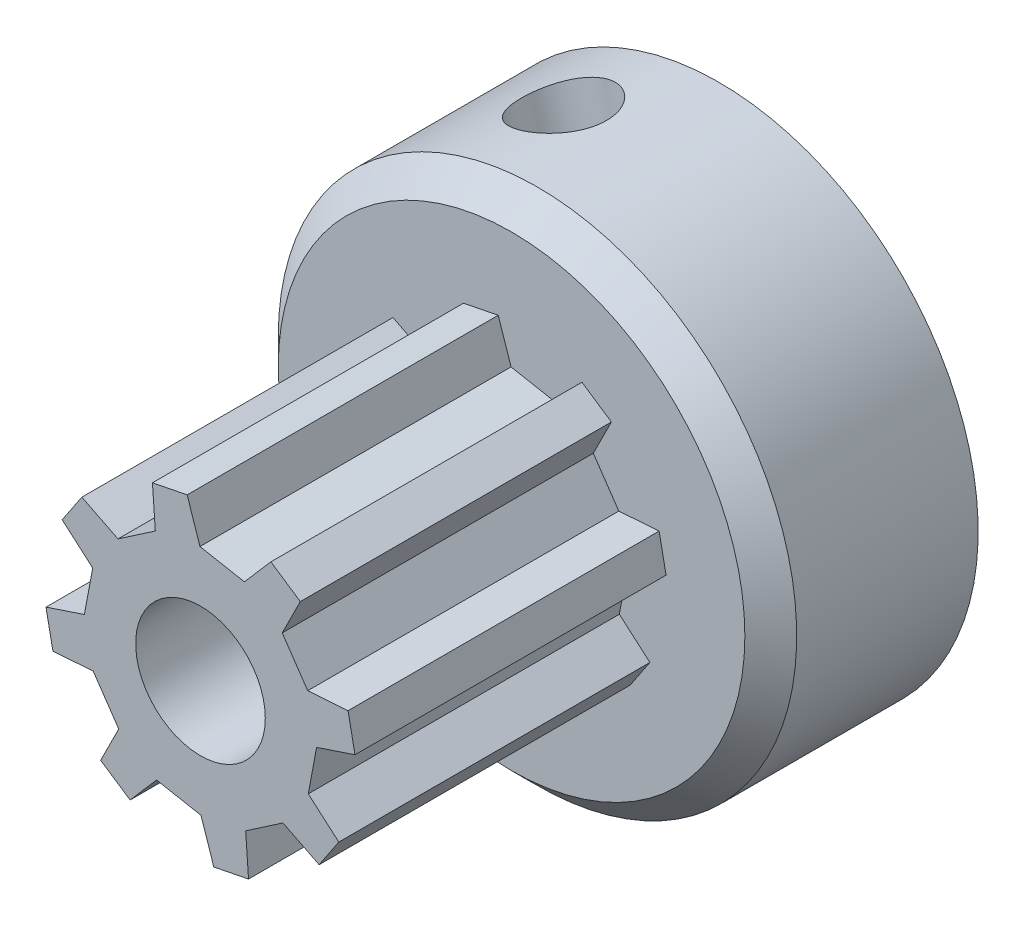
SolidWorks part; units mm, degrees
ref_plane "Front Plane" through (0, 0, 0) normal (0, 0, 1) x (1, 0, 0)
ref_plane "Top Plane" through (0, 0, 0) normal (0, 1, 0) x (1, 0, 0)
ref_plane "Right Plane" through (0, 0, 0) normal (1, 0, 0) x (0, 0, -1)
ref_plane "Plane1" through (0, 0, 15) normal (0, 0, 1) x (1, 0, 0)
sketch "Sketch1" plane through (0, 0, 15) normal (0, 0, 1) x (1, 0, 0)
  line L0 (-0.0203, 4.4797) -> (1.6934, 4.1575)
  line L1 (2.7151, 5.3359) -> (1.6934, 4.1575)
  line L2 (3.8511, 4.5768) -> (2.7151, 5.3359)
  line L3 (3.1533, 3.182) -> (3.8511, 4.5768)
  line L4 (3.1533, 3.182) -> (4.1372, 1.7424)
  line L5 (5.6929, 1.8532) -> (4.1372, 1.7424)
  line L6 (5.9594, 0.5132) -> (5.6929, 1.8532)
  line L7 (4.4797, 0.0203) -> (5.9594, 0.5132)
  line L8 (4.4797, 0.0203) -> (4.1575, -1.6934)
  line L9 (5.3359, -2.7151) -> (4.1575, -1.6934)
  line L10 (4.5768, -3.8511) -> (5.3359, -2.7151)
  line L11 (3.182, -3.1533) -> (4.5768, -3.8511)
  line L12 (3.182, -3.1533) -> (1.7424, -4.1372)
  line L13 (1.8532, -5.6929) -> (1.7424, -4.1372)
  line L14 (0.5132, -5.9594) -> (1.8532, -5.6929)
  line L15 (0.0203, -4.4797) -> (0.5132, -5.9594)
  line L16 (0.0203, -4.4797) -> (-1.6934, -4.1575)
  line L17 (-2.7151, -5.3359) -> (-1.6934, -4.1575)
  line L18 (-3.8511, -4.5768) -> (-2.7151, -5.3359)
  line L19 (-3.1533, -3.182) -> (-3.8511, -4.5768)
  line L20 (-3.1533, -3.182) -> (-4.1372, -1.7424)
  line L21 (-5.6929, -1.8532) -> (-4.1372, -1.7424)
  line L22 (-3.182, 3.1533) -> (-1.7424, 4.1372)
  line L23 (-5.9594, -0.5132) -> (-5.6929, -1.8532)
  line L24 (-4.4797, -0.0203) -> (-5.9594, -0.5132)
  line L25 (-4.4797, -0.0203) -> (-4.1575, 1.6934)
  line L26 (-5.3359, 2.7151) -> (-4.1575, 1.6934)
  line L27 (-4.5768, 3.8511) -> (-5.3359, 2.7151)
  line L28 (-3.182, 3.1533) -> (-4.5768, 3.8511)
  line L29 (-1.1832, 5.8262) -> (-1.2808, 6.3166) construction
  line L30 (3.2831, 4.9564) -> (3.5592, 5.3732) construction
  line L31 (-1.2808, 6.3166) -> (3.5592, 5.3732) construction
  line L32 (-4.9912, 3.3063) -> (-5.4069, 3.5841) construction
  line L33 (-5.8262, -1.1832) -> (-6.3572, -1.2911) construction
  line L34 (-6.3572, -1.2911) -> (-5.4069, 3.5841) construction
  line L104 (-0.0203, 4.4797) -> (-0.5132, 5.9594)
  line L105 (-0.5132, 5.9594) -> (-1.8532, 5.6929)
  line L106 (-1.8532, 5.6929) -> (-1.7424, 4.1372)
  circle A0 centre (0, 0) radius 2.5
  circle A1 centre (0, 0) radius 6.4451 construction
  circle A2 centre (0, 0) radius 5.9869 construction
  circle A3 centre (0, 0) radius 6.4869 construction
  dimension "D4" = 5.097
  dimension "D1" = 97.174
  dimension "D2" = 97.174
  dimension "D3" = 8
extrude "Boss-Extrude1" add sketch "Sketch1" against normal blind 12
sketch "Sketch2" plane through (0, 0, 3) normal (0, 0, -1) x (-1, 0, 0)
  circle A0 centre (0, 0) radius 10
extrude "Boss-Extrude2" add sketch "Sketch2" along normal blind 8
sketch "Sketch9" plane through (0, 0, -5) normal (0, 0, -1) x (-1, 0, 0)
  line L0 (3.8021, 2.565) -> (4.5859, 5.4608)
  line L2 (4.5859, 5.4608) -> (-1.2058, 7.0283)
  line L3 (1.6901, 6.2445) -> (-0.9644, 6.9629) construction
  line L5 (-1.9895, 4.1324) -> (3.8021, 2.565)
  line L8 (-1.2058, 7.0283) -> (-1.9895, 4.1324)
  line L10 (-1.7482, 4.0671) -> (3.5608, 2.6303) construction
  line L11 (1.6901, 6.2445) -> (4.3446, 5.5261) construction
  line L12 (3.7368, 2.3236) -> (4.6512, 5.7021) construction
  line L13 (-2.0548, 3.8911) -> (3.7368, 2.3236) construction
  line L14 (-1.1404, 7.2696) -> (-2.0548, 3.8911) construction
  line L15 (3.5608, 2.6303) -> (4.3446, 5.5261) construction
  line L16 (-0.9644, 6.9629) -> (-1.7482, 4.0671) construction
  line L17 (1.7554, 6.4858) -> (-1.1404, 7.2696) construction
  line L18 (1.7554, 6.4858) -> (4.6512, 5.7021) construction
  dimension "D2" = 0.25
extrude "Cut-Extrude5" cut sketch "Sketch9" against normal blind 6.8
sketch "Sketch10" plane through (0, 0, 3) normal (0, 0, 1) x (1, 0, 0)
  circle A0 centre (0, 0) radius 2.5 construction
  circle A1 centre (0, 0) radius 2.5
extrude "Cut-Extrude6" cut sketch "Sketch10" against normal blind 10
chamfer "Chamfer1" distance 1 angle 45 1 edges at (-10, 0, 3)
sketch "Sketch11" plane through (-0.9063, 3.3487, 0) normal (-0.2612, 0.9653, 0) x (0.9653, 0.2612, 0)
  line L1 (0, 5) -> (0, -1.8) construction
  circle A1 centre (0, 1.6) radius 1.7
extrude "Cut-Extrude7" cut sketch "Sketch11" against normal blind 2 and the other way blind 10
